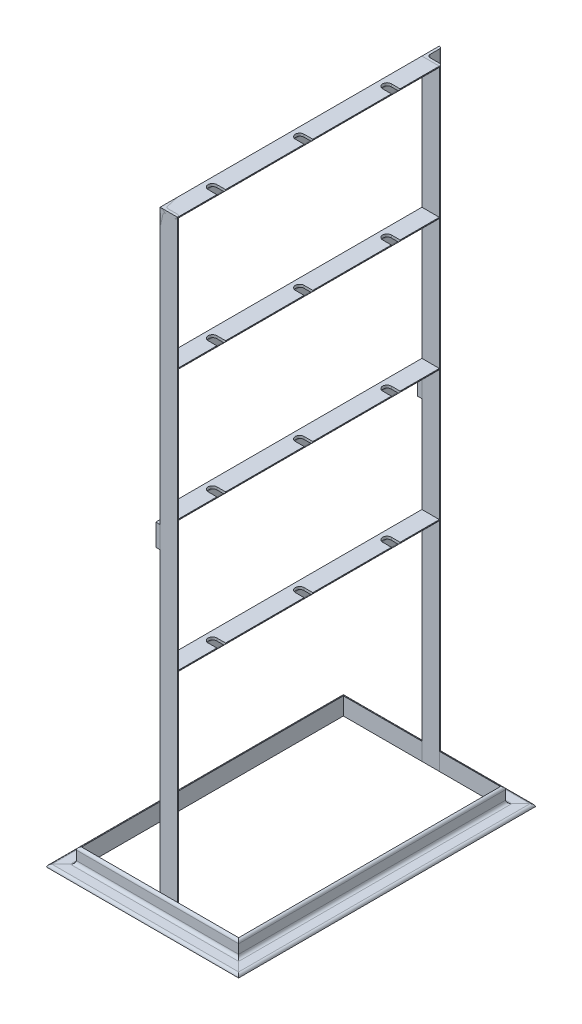
SolidWorks part; units mm, degrees
material "1060 Alloy"
ref_plane "Front Plane" through (0, 0, 0) normal (0, 0, 1) x (1, 0, 0)
ref_plane "Top Plane" through (0, 0, 0) normal (0, 1, 0) x (1, 0, 0)
ref_plane "Right Plane" through (0, 0, 0) normal (1, 0, 0) x (0, 0, -1)
sketch "Sketch22" plane through (0, 0, 0) normal (0, 1, 0) x (1, 0, 0)
  line L1 (-90, 150) -> (90, 150)
  line L2 (-90, 150) -> (-90, -150)
  line L3 (-90, -150) -> (90, -150)
  line L4 (90, 150) -> (90, -150)
  line L5 (-90, 150) -> (90, -150) construction
  line L6 (-90, -150) -> (90, 150) construction
  point P0 (0, 0)
  dimension "D1" = 300
  dimension "D2" = 180
sketch3d "3DSketch1"
  line L0 (0, 0, 150) -> (0, 700, 150)
  line L1 (-90, 0, 150) -> (90, 0, 150) construction
  line L2 (0, 700, 150) -> (0, 700, -150)
  line L3 (0, 700, -150) -> (0, 0, -150)
  line L4 (-90, 0, -150) -> (90, 0, -150) construction
  line L5 (0, 550, 150) -> (0, 550, -150)
  line L6 (0, 400, 150) -> (0, 400, -150)
  line L7 (0, 250, 150) -> (0, 250, -150)
  dimension "D1" = 300
  dimension "D2" = 700
  dimension "D3" = 150
  dimension "D4" = 150
  dimension "D5" = 150
  dimension "D6" = 250
other "Structural Member1"
ref_plane "Plane6" through (90, 0, -150) normal (0, 0, 1) x (1, 0, 0)
sketch "Sketch1" plane through (90, 0, -150) normal (0, 0, 1) x (1, 0, 0)
  line L0 (0, 0) -> (0, 20)
  line L1 (0, 10) -> (3, 10) construction
  line L2 (3, 17) -> (3, 6.5)
  line L3 (6.5, 3) -> (17, 3)
  line L4 (10, 3) -> (10, 0) construction
  line L5 (20, 0) -> (0, 0)
  arc A0 (20, 0) -> (17, 3) centre (17, 0) ccw
  arc A1 (0, 20) -> (3, 17) centre (0, 17) cw
  arc A2 (6.5, 3) -> (3, 6.5) centre (6.5, 6.5) cw
  point P10 (10, 0)
  point P14 (0, 10)
  point P15 (3, 10)
  point P16 (10, 3)
  point P17 (3, 20)
  point P18 (20, 3)
  point P21 (0, 0)
  dimension "D2" = 3
  dimension "D3" = 20
  dimension "Radius_1" = 3.5
  dimension "D1" = 3
other "Structural Member2"
ref_plane "Plane7" through (0, 0, 150) normal (0, 1, 0) x (1, 0, 0)
sketch "Sketch11" plane through (0, 0, 150) normal (0, 1, 0) x (1, 0, 0)
  line L0 (0, 0) -> (0, 20)
  line L1 (0, 10) -> (3, 10) construction
  line L2 (3, 17) -> (3, 6.5)
  line L3 (6.5, 3) -> (17, 3)
  line L4 (10, 3) -> (10, 0) construction
  line L5 (20, 0) -> (0, 0)
  arc A0 (20, 0) -> (17, 3) centre (17, 0) ccw
  arc A1 (0, 20) -> (3, 17) centre (0, 17) cw
  arc A2 (6.5, 3) -> (3, 6.5) centre (6.5, 6.5) cw
  point P10 (10, 0)
  point P14 (0, 10)
  point P15 (3, 10)
  point P16 (10, 3)
  point P17 (3, 20)
  point P18 (20, 3)
  point P21 (0, 0)
  dimension "D2" = 3
  dimension "D3" = 20
  dimension "Radius_1" = 3.5
  dimension "D1" = 3
other "Structural Member3"
ref_plane "Plane8" through (0, 700, 150) normal (0, 0, -1) x (1, 0, 0)
sketch "Sketch12" plane through (0, 700, 150) normal (0, 0, -1) x (1, 0, 0)
  line L0 (0, 0) -> (0, 20)
  line L1 (0, 10) -> (3, 10) construction
  line L2 (3, 17) -> (3, 6.5)
  line L3 (6.5, 3) -> (17, 3)
  line L4 (10, 3) -> (10, 0) construction
  line L5 (20, 0) -> (0, 0)
  arc A0 (20, 0) -> (17, 3) centre (17, 0) ccw
  arc A1 (0, 20) -> (3, 17) centre (0, 17) cw
  arc A2 (6.5, 3) -> (3, 6.5) centre (6.5, 6.5) cw
  point P10 (10, 0)
  point P14 (0, 10)
  point P15 (3, 10)
  point P16 (10, 3)
  point P17 (3, 20)
  point P18 (20, 3)
  point P21 (0, 0)
  dimension "D2" = 3
  dimension "D3" = 20
  dimension "Radius_1" = 3.5
  dimension "D1" = 3
sketch "Sketch23" plane through (0, 700, 0) normal (0, 1, 0) x (1, 0, 0)
  line L0 (0, -150) -> (20, -150) construction
  line L2 (20, 150) -> (20, -150) construction
  line L3 (10, -105) -> (20, -105)
  line L4 (20, -105) -> (20, -95)
  line L5 (20, -95) -> (10, -95)
  arc A0 (10, -95) -> (10, -105) centre (10, -100) ccw
  dimension "D1" = 50
  dimension "D2" = 10
extrude "Cut-Extrude1" cut sketch "Sketch23" against normal blind 512
pattern_linear "LPattern1" count 3 spacing 100 along (0, 0, -1) of "Cut-Extrude1"
sketch "Sketch24" plane through (0, 0, 0) normal (-1, 0, 0) x (0, 0, 1)
  line L0 (130, 700) -> (130, 0) construction
  line L1 (130, 385) -> (150, 385)
  line L2 (130, 385) -> (130, 360)
  line L3 (130, 360) -> (150, 360)
  line L4 (150, 385) -> (150, 360)
  line L5 (150, 0) -> (150, 700) construction
  line L6 (-170, 700) -> (-170, 0) construction
  line L7 (-170, 385) -> (-150, 385)
  line L8 (-170, 385) -> (-170, 360)
  line L9 (-170, 360) -> (-150, 360)
  line L10 (-150, 385) -> (-150, 360)
  line L11 (-150, 700) -> (-150, 0) construction
  line L12 (130, 0) -> (150, 0) construction
  dimension "D1" = 25
  dimension "D2" = 25
  dimension "D3" = 360
  dimension "D4" = 0
extrude "Boss-Extrude2" add sketch "Sketch24" along normal blind 5 separate body
